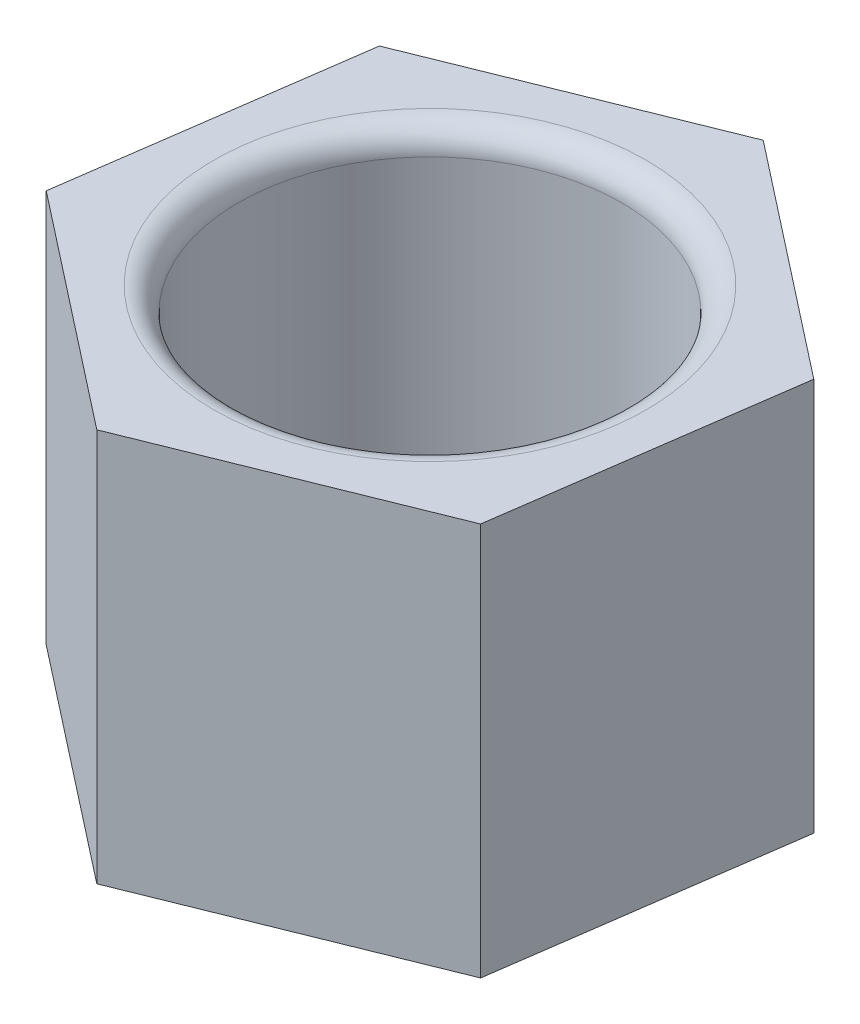
SolidWorks part; units mm, degrees
ref_plane "Front Plane" through (0, 0, 0) normal (0, 0, 1) x (1, 0, 0)
ref_plane "Top Plane" through (0, 0, 0) normal (0, 1, 0) x (1, 0, 0)
ref_plane "Right Plane" through (0, 0, 0) normal (1, 0, 0) x (0, 0, -1)
sketch "Sketch1" plane through (0, 0, 0) normal (0, 1, 0) x (1, 0, 0)
  line L1 (2.3629, -1.8484) -> (2.7822, 1.1221)
  line L2 (2.7822, 1.1221) -> (0.4193, 2.9706)
  line L3 (0.4193, 2.9706) -> (-2.3629, 1.8484)
  line L4 (-2.3629, 1.8484) -> (-2.7822, -1.1221)
  line L5 (-2.7822, -1.1221) -> (-0.4193, -2.9706)
  line L6 (-0.4193, -2.9706) -> (2.3629, -1.8484)
  circle A0 centre (0, 0) radius 2.5981 construction
  dimension "D1" = 6
extrude "Boss-Extrude1" add sketch "Sketch1" along normal blind 4
sketch "Sketch2" plane through (0, 4, 0) normal (0, 1, 0) x (1, 0, 0)
  circle A0 centre (0, 0) radius 1.95
  dimension "D1" = 3.9
extrude "Cut-Extrude1" cut sketch "Sketch2" against normal blind 3
fillet "Fillet1" radius 0.25 1 edges at (0, 4, 1.95)
